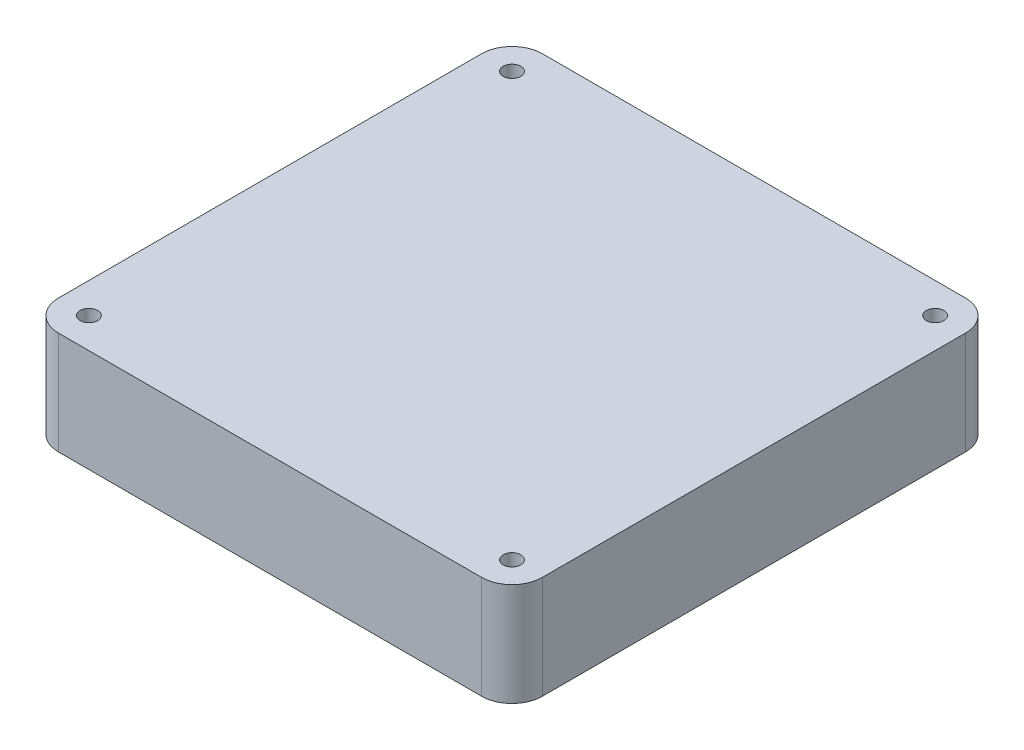
SolidWorks part; units mm, degrees
ref_plane "Front" through (0, 0, 0) normal (0, 0, 1) x (1, 0, 0)
ref_plane "Top" through (0, 0, 0) normal (0, 1, 0) x (1, 0, 0)
ref_plane "Right" through (0, 0, 0) normal (1, 0, 0) x (0, 0, -1)
sketch "Sketch1" plane through (0, 0, 0) normal (0, 1, 0) x (1, 0, 0)
  line L1 (-59.69, 59.69) -> (59.69, 59.69)
  line L2 (-59.69, 59.69) -> (-59.69, -59.69)
  line L3 (-59.69, -59.69) -> (59.69, -59.69)
  line L4 (59.69, 59.69) -> (59.69, -59.69)
  point P4 (0, 59.69)
  point P6 (59.69, 0)
  dimension "D1" = 119.38
  dimension "D2" = 119.38
extrude "Boss-Extrude1" add sketch "Sketch1" along normal blind 25.4
sketch "Sketch2" plane through (0, 25.4, 0) normal (0, 1, 0) x (1, 0, 0)
  line L0 (-59.69, 59.69) -> (-59.69, -59.69) construction
  line L1 (59.69, 59.69) -> (-59.69, 59.69) construction
  line L2 (59.69, -59.69) -> (59.69, 59.69) construction
  line L3 (-59.69, -59.69) -> (59.69, -59.69) construction
  circle A0 centre (-52.19, 52.19) radius 2.165
  circle A1 centre (52.19, 52.19) radius 2.165
  circle A2 centre (52.19, -52.19) radius 2.165
  circle A3 centre (-52.19, -52.19) radius 2.165
  point P16 (0, 0)
  point P17 (0, 0)
  dimension "D1" = 4.33
  dimension "D2" = 4.33
  dimension "D3" = 4.33
  dimension "D4" = 4.33
  dimension "D5" = 7.5
  dimension "D6" = 7.5
  dimension "D7" = 7.5
  dimension "D8" = 7.5
  dimension "D9" = 7.5
  dimension "D10" = 7.5
extrude "Cut-Extrude1" cut sketch "Sketch2" against normal up to next
fillet "Fillet1" radius 7.5 1 edges at (-59.69, 12.7, -59.69)
fillet "Fillet2" radius 7.5 1 edges at (59.69, 12.7, -59.69)
fillet "Fillet3" radius 7.5 2 edges at (-59.69, 12.7, 59.69) (59.69, 12.7, 59.69)
